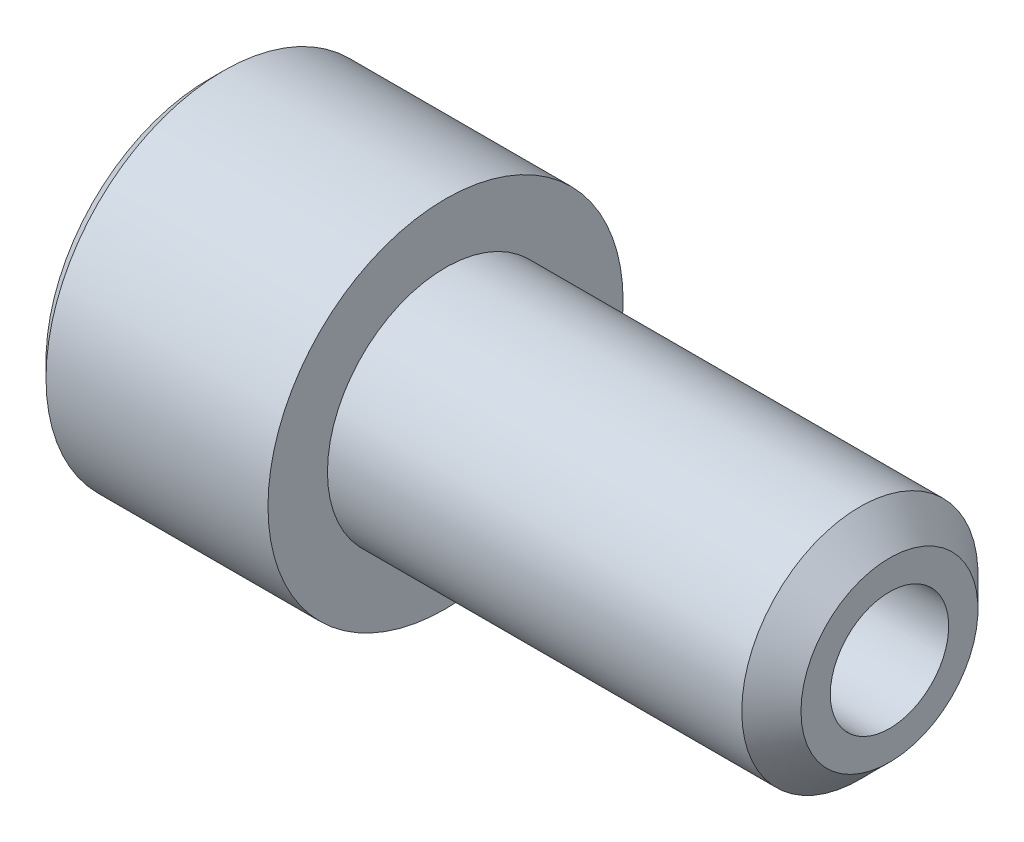
SolidWorks part; units mm, degrees
material "AISI Type 316L stainless steel"
ref_plane "Front Plane" through (0, 0, 0) normal (0, 0, 1) x (1, 0, 0)
ref_plane "Top Plane" through (0, 0, 0) normal (0, 1, 0) x (1, 0, 0)
ref_plane "Right Plane" through (0, 0, 0) normal (1, 0, 0) x (0, 0, -1)
sketch "Sketch1" plane through (0, 0, 0) normal (0, 0, 1) x (1, 0, 0)
  line L0 (-88.7055, 0) -> (96.9812, 0) construction
  line L1 (0, 0) -> (0, 12)
  line L2 (0, 12) -> (16, 12)
  line L4 (46, 0) -> (46, 7.981)
  line L5 (46, 7.981) -> (16, 7.981)
  line L6 (16, 7.981) -> (16, 12)
  line L7 (0, 0) -> (46, 0)
revolve "Revolve1" add sketch "Sketch1" angle 360 about L0
chamfer "Chamfer1" distance 2 angle 45 1 edges at (46, 0, 7.981)
chamfer "Chamfer2" distance 1 angle 45 1 edges at (0, 0, 12)
sketch "Sketch3" plane through (0, 0, 0) normal (1, 0, 0) x (0, 0, -1)
  line L1 (-8.0829, 0) -> (-4.0415, -7)
  line L2 (-4.0415, -7) -> (4.0415, -7)
  line L3 (4.0415, -7) -> (8.0829, 0)
  line L4 (8.0829, 0) -> (4.0415, 7)
  line L5 (4.0415, 7) -> (-4.0415, 7)
  line L6 (-4.0415, 7) -> (-8.0829, 0)
  circle A0 centre (0, 0) radius 7 construction
  dimension "D1" = 14
extrude "Cut-Extrude1" cut sketch "Sketch3" along normal blind 8
chamfer "Chamfer3" distance 1 angle 45 6 edges at (0, 7, 0) (0, 3.5, 6.0622) (0, -3.5, 6.0622) (0, -7, 0) (0, -3.5, -6.0622) (0, 3.5, -6.0622)
sketch "Sketch4" plane through (8, 0, 0) normal (-1, 0, 0) x (0, 0, 1)
  circle A0 centre (0, 0) radius 4
  dimension "D1" = 8
extrude "Cut-Extrude2" cut sketch "Sketch4" against normal through all
